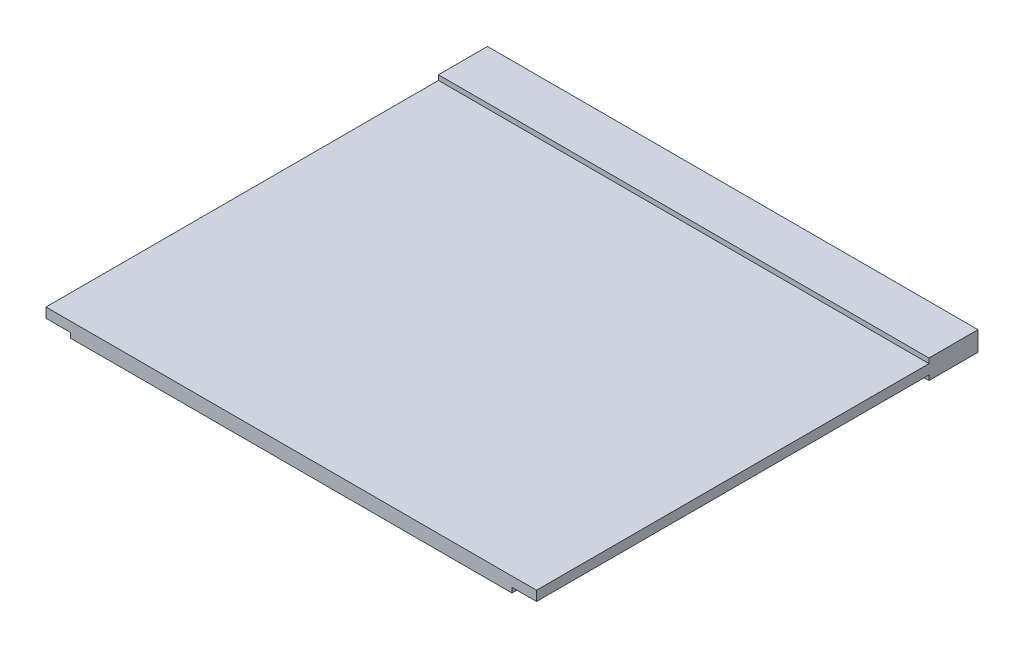
SolidWorks part; units mm, degrees
ref_plane "Piano frontale" through (0, 0, 0) normal (0, 0, 1) x (1, 0, 0)
ref_plane "Piano superiore" through (0, 0, 0) normal (0, 1, 0) x (1, 0, 0)
ref_plane "Piano destro" through (0, 0, 0) normal (1, 0, 0) x (0, 0, -1)
sketch "Schizzo1" plane through (0, 0, 0) normal (0, 0, 1) x (1, 0, 0)
  line L1 (-9.393, 1.1477) -> (40.607, 1.1477)
  line L2 (-9.393, 1.1477) -> (-9.393, -0.8523)
  line L3 (-9.393, -0.8523) -> (40.607, -0.8523)
  line L4 (40.607, 1.1477) -> (40.607, -0.8523)
  dimension "D1" = 2
  dimension "D2" = 50
extrude "Estrusione-Estrusione1" add sketch "Schizzo1" along normal blind 5
sketch "Schizzo2" plane through (0, 0, 5) normal (0, 0, 1) x (1, 0, 0)
  line L0 (-9.393, 1.1477) -> (-9.393, -0.8523) construction
  line L1 (-9.393, 0.6477) -> (40.607, 0.6477)
  line L2 (-9.393, 0.6477) -> (-9.393, -0.3523)
  line L3 (-9.393, -0.3523) -> (40.607, -0.3523)
  line L4 (40.607, 0.6477) -> (40.607, -0.3523)
  line L5 (40.607, -0.8523) -> (40.607, 1.1477) construction
  point P8 (-9.393, 0.1477)
  dimension "D1" = 1
  dimension "D2" = 1
extrude "Estrusione-Estrusione2" add sketch "Schizzo2" along normal blind 40
sketch "Schizzo3" plane through (0, -0.3523, 0) normal (0, -1, 0) x (1, 0, 0)
  line L0 (-9.393, 45) -> (40.607, 45) construction
  line L1 (-6.893, 45) -> (38.107, 45)
  line L2 (-6.893, 45) -> (-6.893, 44)
  line L3 (-6.893, 44) -> (38.107, 44)
  line L4 (38.107, 45) -> (38.107, 44)
  line L5 (-6.893, 42.5) -> (38.107, 42.5)
  line L6 (-6.893, 42.5) -> (-6.893, 41.5)
  line L7 (-6.893, 41.5) -> (38.107, 41.5)
  line L8 (38.107, 42.5) -> (38.107, 41.5)
  line L9 (-6.893, 40) -> (38.107, 40)
  line L10 (-6.893, 40) -> (-6.893, 39)
  line L11 (-6.893, 39) -> (38.107, 39)
  line L12 (38.107, 40) -> (38.107, 39)
  line L13 (-6.893, 37.5) -> (38.107, 37.5)
  line L14 (-6.893, 37.5) -> (-6.893, 36.5)
  line L15 (-6.893, 36.5) -> (38.107, 36.5)
  line L16 (38.107, 37.5) -> (38.107, 36.5)
  line L17 (-6.893, 35) -> (38.107, 35)
  line L18 (-6.893, 35) -> (-6.893, 34)
  line L19 (-6.893, 34) -> (38.107, 34)
  line L20 (38.107, 35) -> (38.107, 34)
  line L21 (-6.893, 32.5) -> (38.107, 32.5)
  line L22 (-6.893, 32.5) -> (-6.893, 31.5)
  line L23 (-6.893, 31.5) -> (38.107, 31.5)
  line L24 (38.107, 32.5) -> (38.107, 31.5)
  line L25 (-6.893, 30) -> (38.107, 30)
  line L26 (-6.893, 30) -> (-6.893, 29)
  line L27 (-6.893, 29) -> (38.107, 29)
  line L28 (38.107, 30) -> (38.107, 29)
  line L29 (-6.893, 27.5) -> (38.107, 27.5)
  line L30 (-6.893, 27.5) -> (-6.893, 26.5)
  line L31 (-6.893, 26.5) -> (38.107, 26.5)
  line L32 (38.107, 27.5) -> (38.107, 26.5)
  line L33 (-6.893, 25) -> (38.107, 25)
  line L34 (-6.893, 25) -> (-6.893, 24)
  line L35 (-6.893, 24) -> (38.107, 24)
  line L36 (38.107, 25) -> (38.107, 24)
  line L37 (-6.893, 22.5) -> (38.107, 22.5)
  line L38 (-6.893, 22.5) -> (-6.893, 21.5)
  line L39 (-6.893, 21.5) -> (38.107, 21.5)
  line L40 (38.107, 22.5) -> (38.107, 21.5)
  line L41 (-6.893, 20) -> (38.107, 20)
  line L42 (-6.893, 20) -> (-6.893, 19)
  line L43 (-6.893, 19) -> (38.107, 19)
  line L44 (38.107, 20) -> (38.107, 19)
  line L45 (-6.893, 17.5) -> (38.107, 17.5)
  line L46 (-6.893, 17.5) -> (-6.893, 16.5)
  line L47 (-6.893, 16.5) -> (38.107, 16.5)
  line L48 (38.107, 17.5) -> (38.107, 16.5)
  point P14 (15.607, 45)
  point P15 (15.607, 40)
  dimension "D1" = 1
  dimension "D2" = 1
  dimension "D3" = 1
  dimension "D4" = 45
  dimension "D5" = 1
  dimension "D6" = 1
  dimension "D7" = 1
  dimension "D8" = 45
  dimension "D9" = 1.5
  dimension "D10" = 1.5
  dimension "D11" = 0
  dimension "D12" = 1.5
  dimension "D13" = 1.5
  dimension "D14" = 1.5
  dimension "D15" = 1
  dimension "D16" = 1
  dimension "D17" = 1
  dimension "D18" = 45
  dimension "D19" = 1
  dimension "D20" = 1
  dimension "D21" = 1
  dimension "D22" = 45
  dimension "D23" = 1.5
  dimension "D24" = 1.5
  dimension "D25" = 1.5
  dimension "D26" = 1.5
  dimension "D27" = 1.5
  dimension "D28" = 1.5
extrude "Estrusione-Estrusione3" add sketch "Schizzo3" along normal blind 0.5
sketch "Schizzo4" plane through (0, -0.3523, 0) normal (0, -1, 0) x (1, 0, 0)
  line L1 (40.607, 45) -> (40.607, 0)
